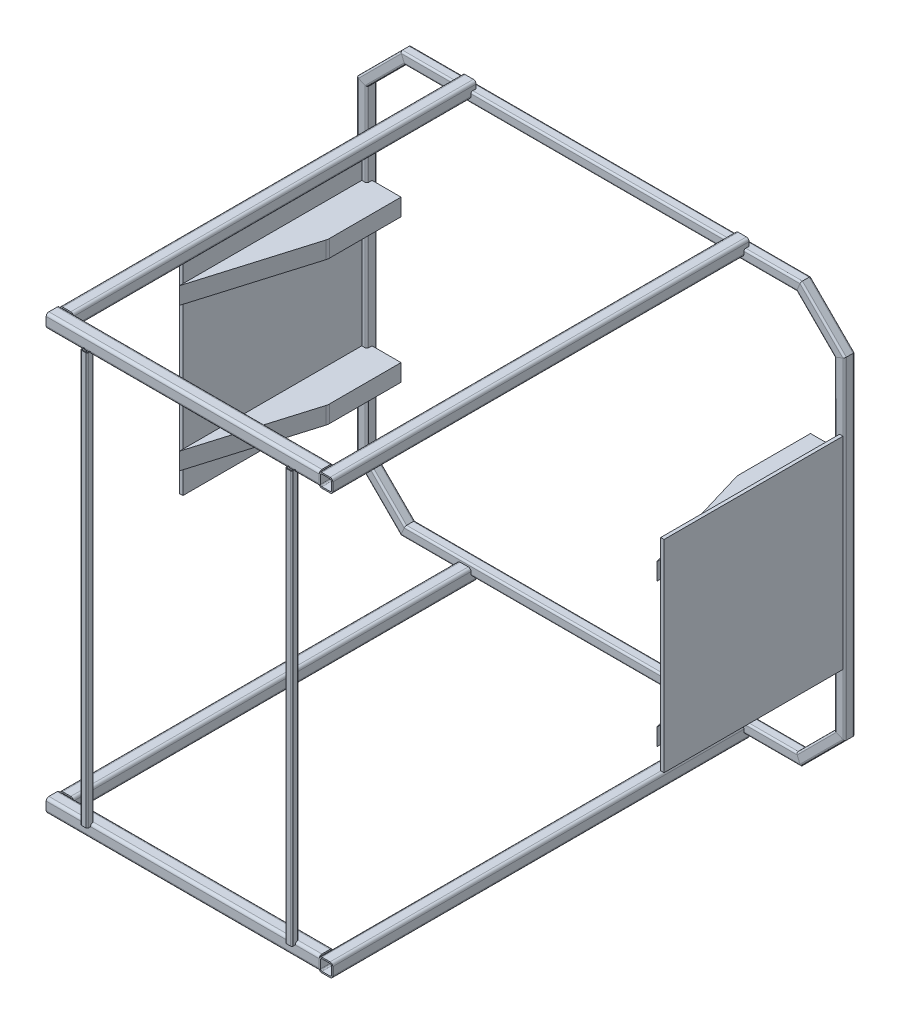
SolidWorks part; units mm, degrees
ref_plane "Płaszczyzna przednia" through (0, 0, 0) normal (0, 0, 1) x (1, 0, 0)
ref_plane "Płaszczyzna górna" through (0, 0, 0) normal (0, 1, 0) x (1, 0, 0)
ref_plane "Płaszczyzna prawa" through (0, 0, 0) normal (1, 0, 0) x (0, 0, -1)
sketch3d "Szkic 3D1"
  line L1 (-580, 600, 0) -> (580, 600, 0)
  line L2 (-700, 480, 0) -> (-700, -480, 0)
  line L3 (-580, -600, 0) -> (580, -600, 0)
  line L4 (700, 480, 0) -> (700, -480, 0)
  line L7 (-580, 600, 0) -> (-700, 480, 0)
  line L8 (580, 600, 0) -> (700, 480, 0)
  line L9 (700, -480, 0) -> (580, -600, 0)
  line L10 (-700, -480, 0) -> (-580, -600, 0)
  line L11 (640, 540, 0) -> (-640, -540, 0) construction
  line L12 (-640, 540, 0) -> (640, -540, 0) construction
  point P0 (0, 0, 0)
  point P18 (0, 0, 0)
  dimension "D11" = 1400
  dimension "D2" = 1200
  dimension "D3" = 120
  dimension "D8" = 120
  dimension "D4" = 120
  dimension "D5" = 120
  dimension "D6" = 120
  dimension "D7" = 120
  dimension "D9" = 120
  dimension "D10" = 120
other "Square tube - configured 30 X 30 X 2.6(1)"
ref_plane "Płaszczyzna1" through (-580, 600, 0) normal (1, 0, 0) x (0, 0, -1)
sketch "Sketch1" plane through (-580, 600, 0) normal (1, 0, 0) x (0, 0, -1)
  line L0 (-9.8, -12.4) -> (9.8, -12.4)
  line L1 (-12.4, -9.8) -> (-12.4, 9.8)
  line L2 (9.8, 12.4) -> (-9.8, 12.4)
  line L3 (12.4, 9.8) -> (12.4, -9.8)
  line L4 (-9.8, -15) -> (9.8, -15)
  line L5 (-15, -9.8) -> (-15, 9.8)
  line L6 (9.8, 15) -> (-9.8, 15)
  line L7 (15, 9.8) -> (15, -9.8)
  arc A0 (15, 9.8) -> (9.8, 15) centre (9.8, 9.8) ccw
  arc A1 (9.8, -15) -> (15, -9.8) centre (9.8, -9.8) ccw
  arc A2 (-15, -9.8) -> (-9.8, -15) centre (-9.8, -9.8) ccw
  arc A3 (-9.8, 15) -> (-15, 9.8) centre (-9.8, 9.8) ccw
  arc A4 (-9.8, 12.4) -> (-12.4, 9.8) centre (-9.8, 9.8) ccw
  arc A5 (12.4, 9.8) -> (9.8, 12.4) centre (9.8, 9.8) ccw
  arc A6 (9.8, -12.4) -> (12.4, -9.8) centre (9.8, -9.8) ccw
  arc A7 (-12.4, -9.8) -> (-9.8, -12.4) centre (-9.8, -9.8) ccw
  point P0 (-15, 0)
  point P1 (15, 0)
  point P2 (0, 15)
  point P3 (0, -15)
  point P4 (0, 0)
  point P5 (-15, -15)
  point P6 (15, -15)
  point P7 (15, 15)
  point P8 (-15, 15)
  point P33 (0, 0)
  dimension "D1" = 5.2
  dimension "Thickness" = 2.6
  dimension "V_leg" = 30
sketch "Szkic1" plane through (0, 615, 0) normal (0, 1, 0) x (1, 0, 0)
  line L0 (-400, 0) -> (-400, -1200)
  line L1 (-400, -1200) -> (400, -1200)
  line L2 (400, -1200) -> (400, 0)
  line L4 (-580, 0) -> (580, 0) construction
  dimension "D1" = 1200
  dimension "D2" = 180
  dimension "D3" = 180
other "Square tube - configured 40 X 40 X 4(1)"
ref_plane "Płaszczyzna2" through (400, 615, 0) normal (0, 0, 1) x (1, 0, 0)
sketch "Sketch13" plane through (400, 615, 0) normal (0, 0, 1) x (1, 0, 0)
  line L0 (-12, -16) -> (12, -16)
  line L1 (-16, -12) -> (-16, 12)
  line L2 (12, 16) -> (-12, 16)
  line L3 (16, 12) -> (16, -12)
  line L4 (-12, -20) -> (12, -20)
  line L5 (-20, -12) -> (-20, 12)
  line L6 (12, 20) -> (-12, 20)
  line L7 (20, 12) -> (20, -12)
  arc A0 (20, 12) -> (12, 20) centre (12, 12) ccw
  arc A1 (12, -20) -> (20, -12) centre (12, -12) ccw
  arc A2 (-20, -12) -> (-12, -20) centre (-12, -12) ccw
  arc A3 (-12, 20) -> (-20, 12) centre (-12, 12) ccw
  arc A4 (-12, 16) -> (-16, 12) centre (-12, 12) ccw
  arc A5 (16, 12) -> (12, 16) centre (12, 12) ccw
  arc A6 (12, -16) -> (16, -12) centre (12, -12) ccw
  arc A7 (-16, -12) -> (-12, -16) centre (-12, -12) ccw
  point P0 (-20, 0)
  point P1 (20, 0)
  point P2 (0, 20)
  point P3 (0, -20)
  point P4 (0, 0)
  point P5 (-20, -20)
  point P6 (20, -20)
  point P7 (20, 20)
  point P8 (-20, 20)
  point P33 (0, 0)
  dimension "D1" = 8
  dimension "Thickness" = 4
  dimension "V_leg" = 40
sketch "Szkic6" plane through (0, -615, 0) normal (0, -1, 0) x (-1, 0, 0)
  line L0 (-400, 0) -> (-400, -1200)
  line L1 (400, 0) -> (400, -1200)
  line L2 (400, -1200) -> (-400, -1200)
  line L4 (580, 0) -> (-580, 0) construction
  dimension "D1" = 180
  dimension "D2" = 180
  dimension "D3" = 1200
other "Square tube - configured 40 X 40 X 4(2)"
ref_plane "Płaszczyzna3" through (400, -615, 0) normal (0, 0, 1) x (-1, 0, 0)
sketch "Sketch14" plane through (400, -615, 0) normal (0, 0, 1) x (-1, 0, 0)
  line L0 (-12, -16) -> (12, -16)
  line L1 (-16, -12) -> (-16, 12)
  line L2 (12, 16) -> (-12, 16)
  line L3 (16, 12) -> (16, -12)
  line L4 (-12, -20) -> (12, -20)
  line L5 (-20, -12) -> (-20, 12)
  line L6 (12, 20) -> (-12, 20)
  line L7 (20, 12) -> (20, -12)
  arc A0 (20, 12) -> (12, 20) centre (12, 12) ccw
  arc A1 (12, -20) -> (20, -12) centre (12, -12) ccw
  arc A2 (-20, -12) -> (-12, -20) centre (-12, -12) ccw
  arc A3 (-12, 20) -> (-20, 12) centre (-12, 12) ccw
  arc A4 (-12, 16) -> (-16, 12) centre (-12, 12) ccw
  arc A5 (16, 12) -> (12, 16) centre (12, 12) ccw
  arc A6 (12, -16) -> (16, -12) centre (12, -12) ccw
  arc A7 (-16, -12) -> (-12, -16) centre (-12, -12) ccw
  point P0 (-20, 0)
  point P1 (20, 0)
  point P2 (0, 20)
  point P3 (0, -20)
  point P4 (0, 0)
  point P5 (-20, -20)
  point P6 (20, -20)
  point P7 (20, 20)
  point P8 (-20, 20)
  point P33 (0, 0)
  dimension "D1" = 8
  dimension "Thickness" = 4
  dimension "V_leg" = 40
sketch "Szkic9" plane through (0, 0, 1220) normal (0, 0, 1) x (1, 0, 0)
  line L0 (300, -603) -> (300, 603)
  line L1 (-420, -603) -> (380, -603) construction
  line L2 (-420, 603) -> (380, 603) construction
  line L3 (-300, -603) -> (-300, 603)
  dimension "D1" = 100
  dimension "D2" = 100
other "Square tube - configured 20 X 20 X 2(1)"
ref_plane "Płaszczyzna4" through (300, -603, 1220) normal (0, 1, 0) x (-1, 0, 0)
sketch "Sketch16" plane through (300, -603, 1220) normal (0, 1, 0) x (-1, 0, 0)
  line L0 (-6, -8) -> (6, -8)
  line L1 (-8, -6) -> (-8, 6)
  line L2 (6, 8) -> (-6, 8)
  line L3 (8, 6) -> (8, -6)
  line L4 (-6, -10) -> (6, -10)
  line L5 (-10, -6) -> (-10, 6)
  line L6 (6, 10) -> (-6, 10)
  line L7 (10, 6) -> (10, -6)
  arc A0 (10, 6) -> (6, 10) centre (6, 6) ccw
  arc A1 (6, -10) -> (10, -6) centre (6, -6) ccw
  arc A2 (-10, -6) -> (-6, -10) centre (-6, -6) ccw
  arc A3 (-6, 10) -> (-10, 6) centre (-6, 6) ccw
  arc A4 (-6, 8) -> (-8, 6) centre (-6, 6) ccw
  arc A5 (8, 6) -> (6, 8) centre (6, 6) ccw
  arc A6 (6, -8) -> (8, -6) centre (6, -6) ccw
  arc A7 (-8, -6) -> (-6, -8) centre (-6, -6) ccw
  point P0 (-10, 0)
  point P1 (10, 0)
  point P2 (0, 10)
  point P3 (0, -10)
  point P4 (0, 0)
  point P5 (-10, -10)
  point P6 (10, -10)
  point P7 (10, 10)
  point P8 (-10, 10)
  point P33 (0, 0)
  dimension "D1" = 4
  dimension "Thickness" = 2
  dimension "V_leg" = 20
ref_plane "Płaszczyzna5" through (0, -230, 0) normal (0, 1, 0) x (1, 0, 0)
ref_plane "Płaszczyzna6" through (0, 230, 0) normal (0, 1, 0) x (1, 0, 0)
sketch "Szkic12" plane through (0, 230, 0) normal (0, 1, 0) x (1, 0, 0)
  line L0 (-610.1726, -45.975) -> (-610.1726, -145.975) construction
  line L1 (-610.1726, -145.975) -> (-760.1726, -545.975) construction
  line L2 (-760.1726, -545.975) -> (-760.1726, -45.975) construction
  line L3 (-760.1726, -45.975) -> (-610.1726, -45.975) construction
  dimension "D1" = 150
  dimension "D2" = 100
  dimension "D3" = 500
sketch "Szkic13" plane through (0, 230, 0) normal (0, 1, 0) x (1, 0, 0)
  line L0 (-600, 0) -> (-600, -210.2129)
  line L1 (-601.2506, -218.7843) -> (-700, -550)
  line L2 (-700, -550) -> (-700, 0)
  line L3 (-700, 0) -> (-600, 0)
  arc A0 (-600, -210.2129) -> (-601.2506, -218.7843) centre (-630, -210.2129) cw
  point P11 (-600, -214.5898)
  dimension "D3" = 30
  dimension "D1" = 350
  dimension "D2" = 550
extrude "Dodanie-wyciągnięcie1" add sketch "Szkic13" against normal blind 50 separate body
pattern_linear "Szyk liniowy1" count 2 spacing 420 along (0, -1, 0) of "Dodanie-wyciągnięcie1"
mirror "Lustro1" about plane through (0, 0, 0) normal (1, 0, 0) of "Dodanie-wyciągnięcie1", "Szyk liniowy1"
sketch "Szkic14" plane through (700, 0, 0) normal (1, 0, 0) x (0, 0, -1)
  line L0 (0, 480) -> (0, -480) construction
  line L1 (0, 285.6525) -> (-539.2626, 285.6525)
  line L2 (0, 285.6525) -> (0, -306.3318)
  line L3 (0, -306.3318) -> (-539.2626, -306.3318)
  line L4 (-539.2626, 285.6525) -> (-539.2626, -306.3318)
extrude "Dodanie-wyciągnięcie2" add sketch "Szkic14" along normal blind 10 separate body
sketch "Szkic15" plane through (-700, 0, 0) normal (-1, 0, 0) x (0, 0, 1)
  line L0 (0, 480) -> (0, -480) construction
  line L1 (0, -307.975) -> (539.2626, -307.975)
  line L2 (0, -307.975) -> (0, 285.6525)
  line L3 (0, 285.6525) -> (539.2626, 285.6525)
  line L4 (539.2626, -307.975) -> (539.2626, 285.6525)
extrude "Dodanie-wyciągnięcie3" add sketch "Szkic15" along normal blind 10 separate body
